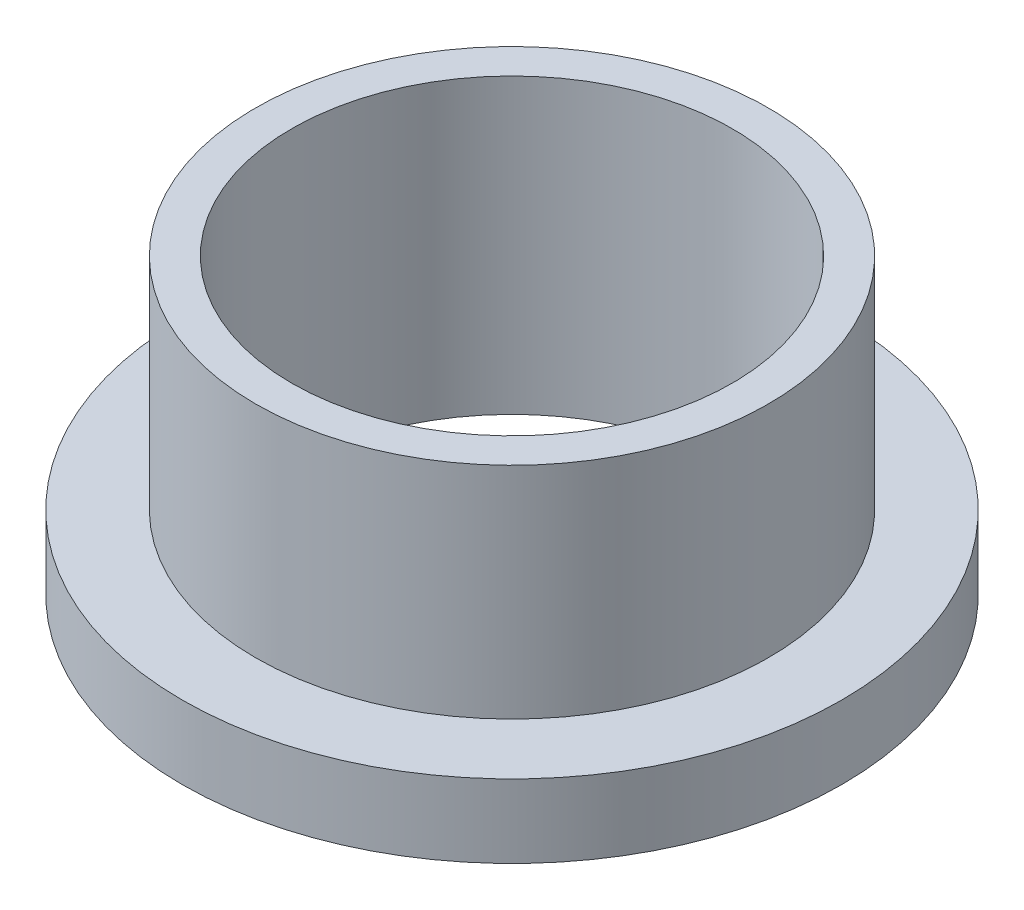
SolidWorks part; units mm, degrees
material "Tin Bearing Bronze"
ref_plane "Front" through (0, 0, 0) normal (0, 0, 1) x (1, 0, 0)
ref_plane "Top" through (0, 0, 0) normal (0, 1, 0) x (1, 0, 0)
ref_plane "Right" through (0, 0, 0) normal (1, 0, 0) x (0, 0, -1)
sketch "Sketch1" plane through (0, 0, 0) normal (0, 1, 0) x (1, 0, 0)
  circle A0 centre (0, 0) radius 9.5504
  circle A1 centre (0, 0) radius 11.1125
  circle A2 centre (0, 0) radius 14.2875
  dimension "ID" = 19.1008
  dimension "OD" = 22.225
  dimension "FlangeOD" = 28.575
sketch "Sketch2" plane through (0, 0, 0) normal (0, 1, 0) x (1, 0, 0)
  circle A0 centre (0, 0) radius 9.5504 construction
  circle A1 centre (0, 0) radius 11.1125 construction
  circle A2 centre (0, 0) radius 9.5504
  circle A3 centre (0, 0) radius 11.1125
extrude "Boss-Extrude1" add sketch "Sketch2" along normal blind 12.7
sketch "Sketch3" plane through (0, 0, 0) normal (0, 1, 0) x (1, 0, 0)
  circle A0 centre (0, 0) radius 14.2875 construction
  circle A1 centre (0, 0) radius 11.1125 construction
  circle A2 centre (0, 0) radius 14.2875
  circle A3 centre (0, 0) radius 11.1125
extrude "Boss-Extrude2" add sketch "Sketch3" along normal blind 3.175
